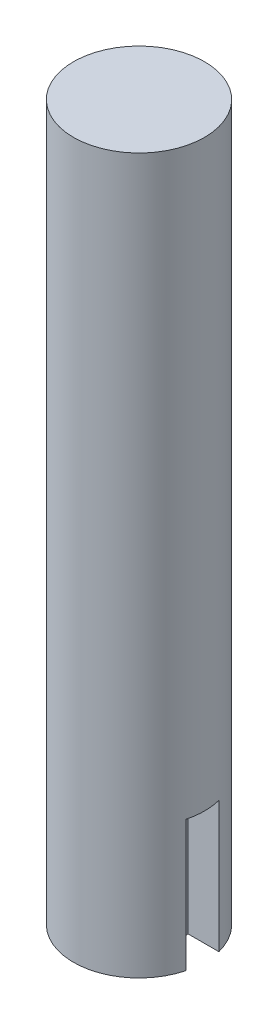
SolidWorks part; units mm, degrees
ref_plane "Front Plane" through (0, 0, 0) normal (0, 0, 1) x (1, 0, 0)
ref_plane "Top Plane" through (0, 0, 0) normal (0, 1, 0) x (1, 0, 0)
ref_plane "Right Plane" through (0, 0, 0) normal (1, 0, 0) x (0, 0, -1)
sketch "Sketch1" plane through (0, 0, 0) normal (0, 1, 0) x (1, 0, 0)
  circle A0 centre (0, 0) radius 10
  dimension "2" = 20
extrude "Boss-Extrude2" add sketch "Sketch1" along normal blind 109
sketch "Sketch3" plane through (0, 0, 0) normal (0, -1, 0) x (1, 0, 0)
  line L1 (5, 2.5) -> (15, 2.5)
  line L2 (5, 2.5) -> (5, -2.5)
  line L3 (5, -2.5) -> (15, -2.5)
  line L4 (15, 2.5) -> (15, -2.5)
  line L5 (5, 2.5) -> (15, -2.5) construction
  line L6 (5, -2.5) -> (15, 2.5) construction
  circle A0 centre (0, 0) radius 10 construction
  point P0 (10, 0)
  dimension "D1" = 10
  dimension "D2" = 5
extrude "Cut-Extrude1" cut sketch "Sketch3" against normal blind 20
